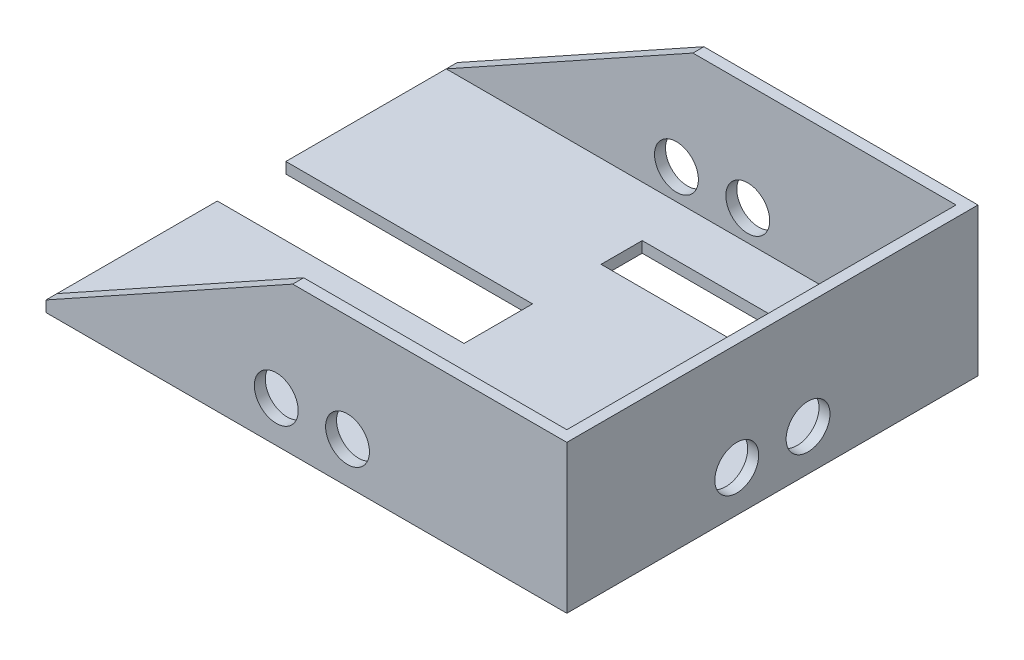
SolidWorks part; units mm, degrees
ref_plane "Front" through (0, 0, 0) normal (0, 0, 1) x (1, 0, 0)
ref_plane "Top" through (0, 0, 0) normal (0, 1, 0) x (1, 0, 0)
ref_plane "Right" through (0, 0, 0) normal (1, 0, 0) x (0, 0, -1)
sketch "Sketch1" plane through (0, 0, 0) normal (0, 1, 0) x (1, 0, 0)
  line L0 (-5, -12.5) -> (-5, 12.5)
  line L1 (95, -75) -> (-95, -75)
  line L2 (95, -75) -> (95, 75)
  line L3 (95, 75) -> (-95, 75)
  line L4 (-95, -75) -> (-95, -12.5)
  line L5 (0, 75) -> (0, -75) construction
  line L6 (95, 0) -> (-95, 0) construction
  line L7 (-5, 12.5) -> (-95, 12.5)
  line L8 (-5, -12.5) -> (-95, -12.5)
  line L9 (-95, 12.5) -> (-95, 75)
  point P0 (0, 0)
  point P7 (-5, 0)
  dimension "D1" = 190
  dimension "D2" = 150
  dimension "D3" = 25
  dimension "D4" = 100
extrude "Boss-Extrude1" add sketch "Sketch1" along normal blind 4
sketch "Sketch2" plane through (0, 0, 75) normal (0, 0, 1) x (1, 0, 0)
  line L0 (95, 4) -> (95, 54)
  line L1 (95, 54) -> (-5, 54)
  line L2 (-5, 54) -> (-95, 4)
  line L3 (-95, 4) -> (95, 4)
  dimension "D1" = 50
  dimension "D2" = 100
extrude "Boss-Extrude2" add sketch "Sketch2" against normal blind 4
mirror "Mirror1" about plane through (0, 0, 0) normal (0, 0, 1) of "Boss-Extrude2"
sketch "Sketch3" plane through (95, 0, 0) normal (1, 0, 0) x (0, 0, -1)
  line L0 (-71, 54) -> (71, 54)
  line L1 (71, 4) -> (71, 54) construction
  line L2 (71, 54) -> (71, 4)
  line L3 (71, 4) -> (-71, 4)
  line L4 (-71, 4) -> (-71, 54)
extrude "Boss-Extrude3" add sketch "Sketch3" against normal blind 4
sketch "Sketch4" plane through (0, 0, 0) normal (0, -1, 0) x (1, 0, 0)
  line L0 (95, 75) -> (95, -75) construction
  line L1 (75, 52.5) -> (-5, 52.5)
  line L2 (75, 52.5) -> (75, 37.5)
  line L3 (75, 37.5) -> (-5, 37.5)
  line L4 (-5, 52.5) -> (-5, 37.5)
  line L5 (35, 37.5) -> (35, 52.5) construction
  line L6 (75, 45) -> (-5, 45) construction
  line L7 (-95, 75) -> (95, 75) construction
  point P0 (35, 45)
  dimension "D1" = 60
  dimension "D2" = 30
  dimension "D3" = 80
  dimension "D4" = 15
extrude "Cut-Extrude1" cut sketch "Sketch4" against normal blind 4 contours L3 L4 L1 L2
mirror "Mirror2" about plane through (0, 0, 0) normal (0, 0, 1) of "Cut-Extrude1"
sketch "Sketch5" plane through (95, 0, 0) normal (1, 0, 0) x (0, 0, -1)
  line L0 (-13, 15) -> (13, 15) construction
  circle A0 centre (-13, 15) radius 8
  circle A1 centre (13, 15) radius 8
  point P2 (0, 15)
  dimension "D1" = 26
  dimension "D2" = 15
  dimension "D3" = 0
extrude "Cut-Extrude2" cut sketch "Sketch5" against normal blind 4
sketch "Sketch6" plane through (0, 0, -75) normal (0, 0, -1) x (-1, 0, 0)
  line L0 (-15, 15) -> (11, 15) construction
  line L1 (-95, 54) -> (-95, 0) construction
  line L2 (-95, 0) -> (95, 0) construction
  circle A0 centre (-15, 15) radius 8
  circle A1 centre (11, 15) radius 8
  dimension "D3" = 15
  dimension "D1" = 26
  dimension "D2" = 80
extrude "Cut-Extrude3" cut sketch "Sketch6" against normal blind 4
mirror "Mirror3" about plane through (0, 0, 0) normal (0, 0, 1) of "Cut-Extrude3"
